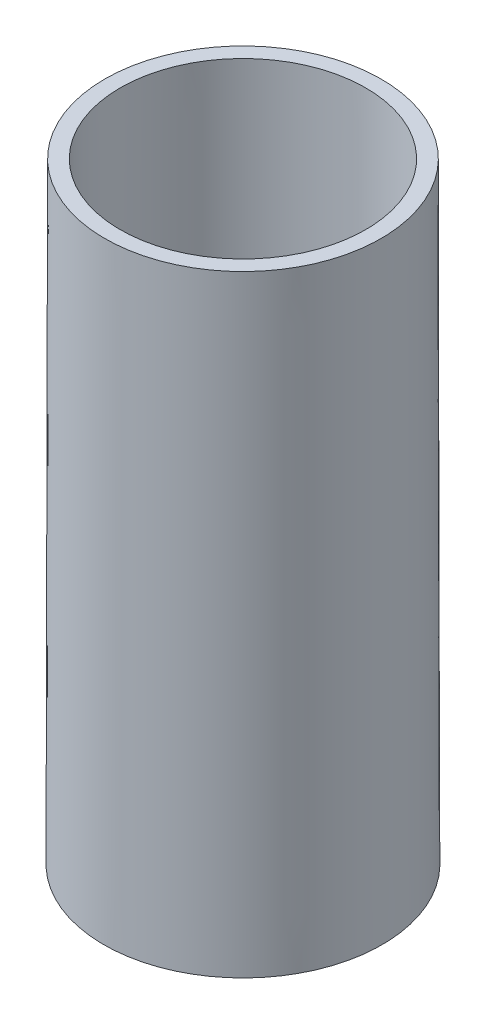
SolidWorks part; units mm, degrees
ref_plane "Front Plane" through (0, 0, 0) normal (0, 0, 1) x (1, 0, 0)
ref_plane "Top Plane" through (0, 0, 0) normal (0, 1, 0) x (1, 0, 0)
ref_plane "Right Plane" through (0, 0, 0) normal (1, 0, 0) x (0, 0, -1)
sketch "Sketch1" plane through (0, 0, 0) normal (0, 0, 1) x (1, 0, 0)
  line L0 (0, 0) -> (49.435, 0)
  line L1 (49.435, 0) -> (50, -318.3914)
  line L2 (50, -318.3914) -> (44.4843, -318.3914)
  line L3 (44.4843, -318.3914) -> (43.9301, -6.0882)
  line L4 (43.9301, -6.0882) -> (0, -6.0882)
  line L5 (0, -6.0882) -> (0, 0)
  line L6 (0, 0) -> (0, -318.3914) construction
  dimension "D1" = 49.435
  dimension "D2" = 50
revolve "Revolve1" add sketch "Sketch1" angle 360 about L6
sketch "Sketch2" plane through (0, 0, 0) normal (0, 1, 0) x (1, 0, 0)
  circle A0 centre (0, 0) radius 88.4242
extrude "Cut-Extrude1" cut sketch "Sketch2" against normal blind 99
